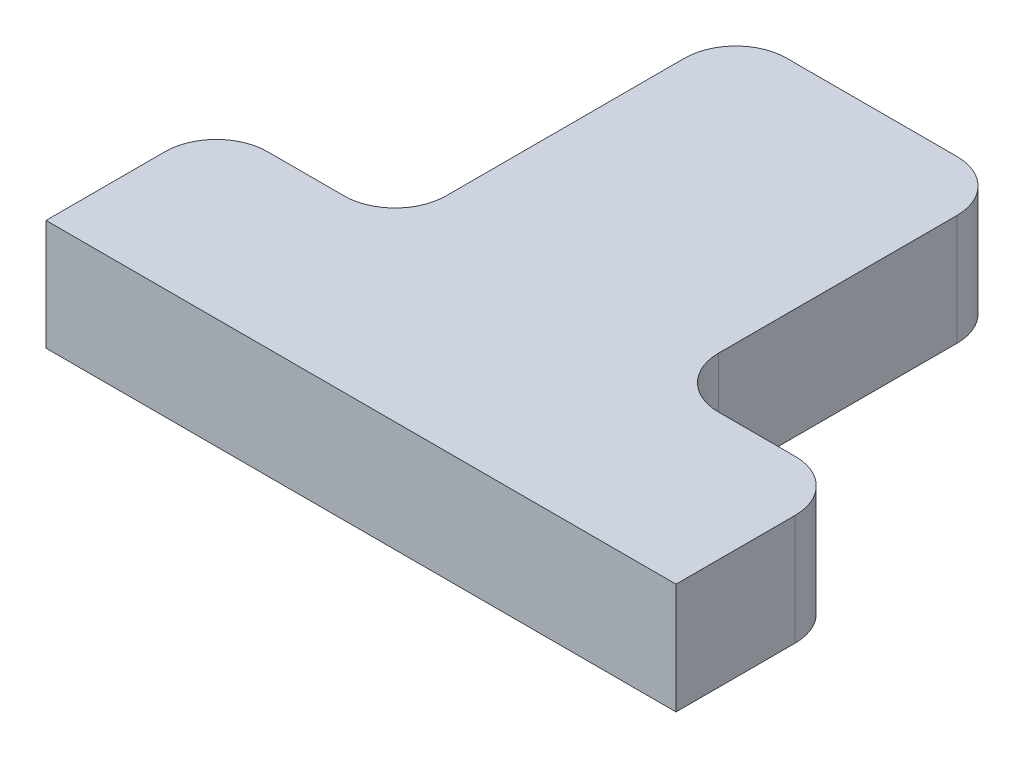
SolidWorks part; units mm, degrees
ref_plane "Front Plane" through (0, 0, 0) normal (0, 0, 1) x (1, 0, 0)
ref_plane "Top Plane" through (0, 0, 0) normal (0, 1, 0) x (1, 0, 0)
ref_plane "Right Plane" through (0, 0, 0) normal (1, 0, 0) x (0, 0, -1)
sketch "Sketch1" plane through (0, 0, 0) normal (0, 1, 0) x (1, 0, 0)
  line L0 (8, 30) -> (8, 0) construction
  line L1 (0, 0) -> (16, 0)
  line L2 (0, 10) -> (0, 30)
  line L3 (0, 30) -> (16, 30)
  line L4 (16, 10) -> (16, 30)
  line L5 (16, 0) -> (26.5, 0)
  line L6 (0, 0) -> (-10.5, 0)
  line L7 (16, 10) -> (26.5, 10)
  line L8 (26.5, 0) -> (26.5, 10)
  line L9 (-10.5, 0) -> (-10.5, 10)
  line L10 (0, 10) -> (-10.5, 10)
  point P13 (0, 0)
  dimension "D1" = 16
  dimension "D2" = 30
  dimension "D3" = 20
  dimension "D4" = 10.5
  dimension "D5" = 8
  dimension "D6" = 18.5
  dimension "D7" = 37
extrude "Boss-Extrude1" add sketch "Sketch1" along normal blind 6.5 contours L2 L3 L4 L7 L8 L5 L1 L6 L9 L10
fillet "Fillet1" radius 3 6 edges at (0, 3.25, -10) (16, 3.25, -10) (16, 3.25, -30) (0, 3.25, -30) (-10.5, 3.25, -10) (26.5, 3.25, -10)
